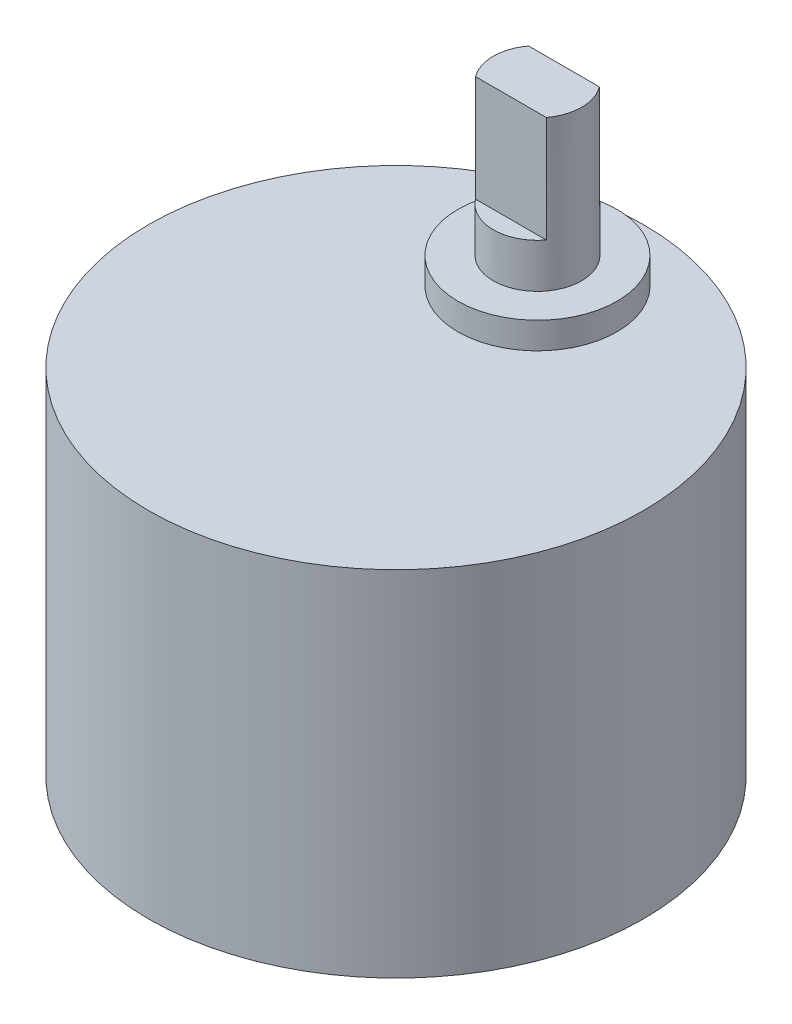
SolidWorks part; units mm, degrees
material "2024 Alloy"
ref_plane "Front Plane" through (0, 0, 0) normal (0, 0, 1) x (1, 0, 0)
ref_plane "Top Plane" through (0, 0, 0) normal (0, 1, 0) x (1, 0, 0)
ref_plane "Right Plane" through (0, 0, 0) normal (1, 0, 0) x (0, 0, -1)
sketch "Sketch1" plane through (0, 0, 0) normal (0, 1, 0) x (1, 0, 0)
  circle A0 centre (0, 0) radius 14
extrude "Boss-Extrude1" add sketch "Sketch1" along normal blind 20
sketch "Sketch3" plane through (0, 20, 0) normal (0, 1, 0) x (1, 0, 0)
  circle A0 centre (0, 8) radius 4.5
extrude "Boss-Extrude2" add sketch "Sketch3" along normal blind 1.5
sketch "Sketch4" plane through (0, 21.5, 0) normal (0, 1, 0) x (1, 0, 0)
  circle A0 centre (0, 8) radius 2.5
extrude "Boss-Extrude3" add sketch "Sketch4" along normal blind 8.5
sketch "Sketch5" plane through (0, 30, 0) normal (0, 1, 0) x (1, 0, 0)
  line L4 (2, 9.5) -> (-2, 9.5)
  line L5 (-2, 6.5) -> (2, 6.5)
  circle A0 centre (0, 8) radius 2.5 construction
  arc A1 (2, 6.5) -> (-2, 6.5) centre (0, 8) cw
  arc A2 (2, 9.5) -> (-2, 9.5) centre (0, 8) ccw
  point P1 (0, 8)
extrude "Cut-Extrude1" cut sketch "Sketch5" against normal blind 6
